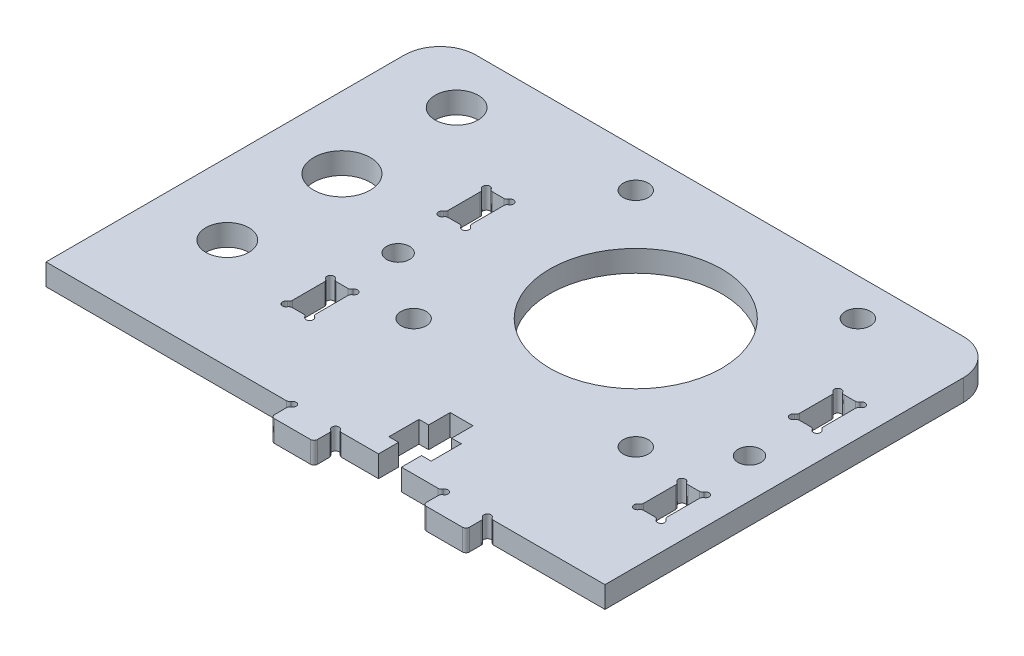
SolidWorks part; units mm, degrees
material "Plain Carbon Steel"
ref_plane "Front Plane" through (0, 0, 0) normal (0, 0, 1) x (1, 0, 0)
ref_plane "Top Plane" through (0, 0, 0) normal (0, 1, 0) x (1, 0, 0)
ref_plane "Right Plane" through (0, 0, 0) normal (1, 0, 0) x (0, 0, -1)
sketch "Sketch1" plane through (0, 0, 0) normal (0, 1, 0) x (1, 0, 0)
  line L0 (365.2434, 1060.953) -> (365.2434, 1056.485)
  line L1 (367.6773, 1061.819) -> (366.1094, 1061.819)
  line L2 (318.6373, 1061.819) -> (317.0694, 1061.819)
  line L3 (294.3734, 1022.1903) -> (327.9073, 1022.1903)
  line L4 (294.3734, 1072.1903) -> (294.3734, 1022.1903)
  line L5 (316.2034, 1039.1936) -> (316.2034, 1034.7256)
  line L6 (318.6373, 1040.0596) -> (317.0694, 1040.0596)
  line L7 (368.5433, 1034.7256) -> (368.5433, 1039.1936)
  line L8 (366.1094, 1033.8596) -> (367.6773, 1033.8596)
  line L9 (365.2434, 1039.1936) -> (365.2434, 1034.7256)
  line L10 (367.6773, 1040.0596) -> (366.1094, 1040.0596)
  line L11 (319.5033, 1056.485) -> (319.5033, 1060.953)
  line L12 (317.0694, 1055.619) -> (318.6373, 1055.619)
  line L13 (316.2034, 1060.953) -> (316.2034, 1056.485)
  line L14 (319.5033, 1034.7256) -> (319.5033, 1039.1936)
  line L15 (317.0694, 1033.8596) -> (318.6373, 1033.8596)
  line L16 (366.1094, 1055.619) -> (367.6773, 1055.619)
  line L17 (343.9733, 1022.1903) -> (349.1073, 1022.1903)
  line L18 (343.9733, 1024.9903) -> (343.9733, 1022.1903)
  line L19 (345.3233, 1024.9903) -> (343.9733, 1024.9903)
  line L20 (345.3233, 1029.1903) -> (345.3233, 1024.9903)
  line L21 (343.9733, 1029.1903) -> (345.3233, 1029.1903)
  line L22 (343.9733, 1032.1903) -> (343.9733, 1029.1903)
  line L23 (367.3733, 1077.1903) -> (299.3733, 1077.1903)
  line L24 (372.3733, 1022.1903) -> (372.3733, 1072.1903)
  line L25 (356.8394, 1022.1903) -> (372.3733, 1022.1903)
  line L26 (355.9733, 1019.6902) -> (355.9733, 1021.3243)
  line L27 (350.4733, 1019.1902) -> (355.4733, 1019.1902)
  line L28 (349.9733, 1021.3243) -> (349.9733, 1019.6902)
  line L29 (340.7733, 1032.1903) -> (343.9733, 1032.1903)
  line L30 (340.7733, 1029.1903) -> (340.7733, 1032.1903)
  line L31 (339.4233, 1029.1903) -> (340.7733, 1029.1903)
  line L32 (339.4233, 1024.9903) -> (339.4233, 1029.1903)
  line L33 (340.7733, 1024.9903) -> (339.4233, 1024.9903)
  line L34 (340.7733, 1022.1903) -> (340.7733, 1024.9903)
  line L35 (335.6394, 1022.1903) -> (340.7733, 1022.1903)
  line L36 (368.5433, 1056.485) -> (368.5433, 1060.953)
  line L37 (334.7733, 1019.6902) -> (334.7733, 1021.3243)
  line L38 (329.2733, 1019.1902) -> (334.2733, 1019.1902)
  line L39 (328.7733, 1021.3243) -> (328.7733, 1019.6902)
  line L40 (372.3733, 1022.1903) -> (312.3734, 1022.1903) construction
  line L41 (317.8533, 1047.1903) -> (317.8533, 1081.5508) construction
  line L42 (368.0078, 1047.1903) -> (368.0078, 1096.6784) construction
  line L43 (372.3733, 1047.8425) -> (312.3734, 1047.8425) construction
  line L44 (372.3733, 1047.1903) -> (312.3734, 1047.1903) construction
  line L45 (304.3733, 1051.4903) -> (304.3733, 1061.836) construction
  line L46 (342.3733, 1056.4903) -> (342.3733, 1061.5411) construction
  line L50 (372.3733, 1036.9659) -> (312.3734, 1036.9659) construction
  line L51 (372.3733, 1058.719) -> (312.3734, 1058.719) construction
  line L52 (342.3733, 1056.4903) -> (290.0337, 1056.4903) construction
  line L53 (325.3733, 1053.4903) -> (295.5151, 1053.4903) construction
  arc A0 (299.3733, 1077.1903) -> (294.3734, 1072.1903) centre (299.3733, 1072.1903) ccw
  arc A1 (364.9934, 1056.052) -> (365.6764, 1055.369) centre (365.2434, 1055.619) ccw
  arc A2 (364.9934, 1056.052) -> (365.2434, 1056.485) centre (364.7434, 1056.485) ccw
  arc A3 (365.6764, 1062.069) -> (366.1094, 1061.819) centre (366.1094, 1062.319) ccw
  arc A4 (316.6364, 1062.069) -> (317.0694, 1061.819) centre (317.0694, 1062.319) ccw
  arc A5 (365.2434, 1060.953) -> (364.9934, 1061.386) centre (364.7434, 1060.953) ccw
  arc A6 (365.6764, 1062.069) -> (364.9934, 1061.386) centre (365.2434, 1061.819) ccw
  arc A7 (366.1094, 1055.619) -> (365.6764, 1055.369) centre (366.1094, 1055.119) ccw
  arc A8 (315.9534, 1034.2926) -> (316.2034, 1034.7256) centre (315.7034, 1034.7256) ccw
  arc A9 (316.2034, 1039.1936) -> (315.9534, 1039.6266) centre (315.7034, 1039.1936) ccw
  arc A10 (316.6364, 1040.3096) -> (315.9534, 1039.6266) centre (316.2034, 1040.0596) ccw
  arc A11 (316.6364, 1040.3096) -> (317.0694, 1040.0596) centre (317.0694, 1040.5596) ccw
  arc A12 (367.6773, 1061.819) -> (368.1103, 1062.069) centre (367.6773, 1062.319) ccw
  arc A13 (368.7933, 1039.6266) -> (368.1103, 1040.3096) centre (368.5433, 1040.0596) ccw
  arc A14 (368.7933, 1039.6266) -> (368.5433, 1039.1936) centre (369.0433, 1039.1936) ccw
  arc A15 (368.5433, 1034.7256) -> (368.7933, 1034.2926) centre (369.0433, 1034.7256) ccw
  arc A16 (368.1103, 1033.6096) -> (368.7933, 1034.2926) centre (368.5433, 1033.8596) ccw
  arc A17 (368.1103, 1033.6096) -> (367.6773, 1033.8596) centre (367.6773, 1033.3596) ccw
  arc A18 (366.1094, 1033.8596) -> (365.6764, 1033.6096) centre (366.1094, 1033.3596) ccw
  arc A19 (364.9934, 1034.2926) -> (365.6764, 1033.6096) centre (365.2434, 1033.8596) ccw
  arc A20 (364.9934, 1034.2926) -> (365.2434, 1034.7256) centre (364.7434, 1034.7256) ccw
  arc A21 (365.2434, 1039.1936) -> (364.9934, 1039.6266) centre (364.7434, 1039.1936) ccw
  arc A22 (365.6764, 1040.3096) -> (364.9934, 1039.6266) centre (365.2434, 1040.0596) ccw
  arc A23 (365.6764, 1040.3096) -> (366.1094, 1040.0596) centre (366.1094, 1040.5596) ccw
  arc A24 (367.6773, 1040.0596) -> (368.1103, 1040.3096) centre (367.6773, 1040.5596) ccw
  arc A25 (319.7533, 1061.386) -> (319.0703, 1062.069) centre (319.5033, 1061.819) ccw
  arc A26 (319.7533, 1061.386) -> (319.5033, 1060.953) centre (320.0033, 1060.953) ccw
  arc A27 (319.5033, 1056.485) -> (319.7533, 1056.052) centre (320.0033, 1056.485) ccw
  arc A28 (319.0703, 1055.369) -> (319.7533, 1056.052) centre (319.5033, 1055.619) ccw
  arc A29 (319.0703, 1055.369) -> (318.6373, 1055.619) centre (318.6373, 1055.119) ccw
  arc A30 (317.0694, 1055.619) -> (316.6364, 1055.369) centre (317.0694, 1055.119) ccw
  arc A31 (315.9534, 1056.052) -> (316.6364, 1055.369) centre (316.2034, 1055.619) ccw
  arc A32 (315.9534, 1056.052) -> (316.2034, 1056.485) centre (315.7034, 1056.485) ccw
  arc A33 (316.2034, 1060.953) -> (315.9534, 1061.386) centre (315.7034, 1060.953) ccw
  arc A34 (316.6364, 1062.069) -> (315.9534, 1061.386) centre (316.2034, 1061.819) ccw
  circle A35 centre (366.8933, 1047.8425) radius 1.6
  circle A36 centre (357.8733, 1071.9903) radius 1.75
  circle A37 centre (357.8733, 1040.9903) radius 1.75
  arc A38 (318.6373, 1061.819) -> (319.0703, 1062.069) centre (318.6373, 1062.319) ccw
  arc A39 (319.7533, 1039.6266) -> (319.0703, 1040.3096) centre (319.5033, 1040.0596) ccw
  arc A40 (319.7533, 1039.6266) -> (319.5033, 1039.1936) centre (320.0033, 1039.1936) ccw
  arc A41 (319.5033, 1034.7256) -> (319.7533, 1034.2926) centre (320.0033, 1034.7256) ccw
  arc A42 (319.0703, 1033.6096) -> (319.7533, 1034.2926) centre (319.5033, 1033.8596) ccw
  arc A43 (319.0703, 1033.6096) -> (318.6373, 1033.8596) centre (318.6373, 1033.3596) ccw
  arc A44 (315.9534, 1034.2926) -> (316.6364, 1033.6096) centre (316.2034, 1033.8596) ccw
  arc A45 (349.1073, 1022.1903) -> (349.5403, 1022.4403) centre (349.1073, 1022.6903) ccw
  arc A46 (318.6373, 1040.0596) -> (319.0703, 1040.3096) centre (318.6373, 1040.5596) ccw
  circle A47 centre (304.3733, 1053.4903) radius 3.95
  circle A48 centre (342.3733, 1056.4903) radius 12
  arc A49 (372.3733, 1072.1903) -> (367.3733, 1077.1903) centre (367.3733, 1072.1903) ccw
  arc A50 (356.4064, 1022.4403) -> (356.8394, 1022.1903) centre (356.8394, 1022.6903) ccw
  arc A51 (356.4064, 1022.4403) -> (355.7233, 1021.7573) centre (355.9733, 1022.1903) ccw
  arc A52 (355.9733, 1021.3243) -> (355.7233, 1021.7573) centre (355.4733, 1021.3243) ccw
  arc A53 (355.4733, 1019.1902) -> (355.9733, 1019.6902) centre (355.4733, 1019.6902) ccw
  arc A54 (349.9733, 1019.6902) -> (350.4733, 1019.1902) centre (350.4733, 1019.6902) ccw
  arc A55 (350.2233, 1021.7573) -> (349.9733, 1021.3243) centre (350.4733, 1021.3243) ccw
  arc A56 (350.2233, 1021.7573) -> (349.5403, 1022.4403) centre (349.9733, 1022.1903) ccw
  arc A57 (317.0694, 1033.8596) -> (316.6364, 1033.6096) centre (317.0694, 1033.3596) ccw
  arc A58 (327.9073, 1022.1903) -> (328.3403, 1022.4403) centre (327.9073, 1022.6903) ccw
  arc A59 (335.2063, 1022.4403) -> (335.6394, 1022.1903) centre (335.6394, 1022.6903) ccw
  circle A60 centre (326.8733, 1071.9903) radius 1.75
  circle A61 centre (326.8733, 1040.9903) radius 1.75
  circle A62 centre (317.8533, 1047.8495) radius 1.6
  arc A63 (368.7933, 1061.386) -> (368.1103, 1062.069) centre (368.5433, 1061.819) ccw
  arc A64 (368.5433, 1056.485) -> (368.7933, 1056.052) centre (369.0433, 1056.485) ccw
  arc A65 (335.2063, 1022.4403) -> (334.5233, 1021.7573) centre (334.7733, 1022.1903) ccw
  arc A66 (334.7733, 1021.3243) -> (334.5233, 1021.7573) centre (334.2733, 1021.3243) ccw
  arc A67 (368.7933, 1061.386) -> (368.5433, 1060.953) centre (369.0433, 1060.953) ccw
  arc A68 (328.7733, 1019.6902) -> (329.2733, 1019.1902) centre (329.2733, 1019.6902) ccw
  arc A69 (368.1103, 1055.369) -> (368.7933, 1056.052) centre (368.5433, 1055.619) ccw
  arc A70 (368.1103, 1055.369) -> (367.6773, 1055.619) centre (367.6773, 1055.119) ccw
  arc A71 (329.0233, 1021.7573) -> (328.3403, 1022.4403) centre (328.7733, 1022.1903) ccw
  arc A72 (334.2733, 1019.1902) -> (334.7733, 1019.6902) centre (334.2733, 1019.6902) ccw
  arc A73 (329.0233, 1021.7573) -> (328.7733, 1021.3243) centre (329.2733, 1021.3243) ccw
  circle A75 centre (304.3733, 1069.4903) radius 3
  circle A76 centre (304.3733, 1037.4903) radius 3
  point P193 (317.8533, 1047.8495)
  point P202 (368.5433, 1036.9596)
  point P205 (368.5433, 1058.719)
  point P208 (316.2034, 1058.719)
  point P209 (0, 0)
  point P211 (319.5033, 1036.9596)
  dimension "D3" = 14.7757
  dimension "D1" = 25
  dimension "D2" = 25.6522
  dimension "D4" = 36.5287
extrude "Boss-Extrude1" add sketch "Sketch1" along normal blind 3
